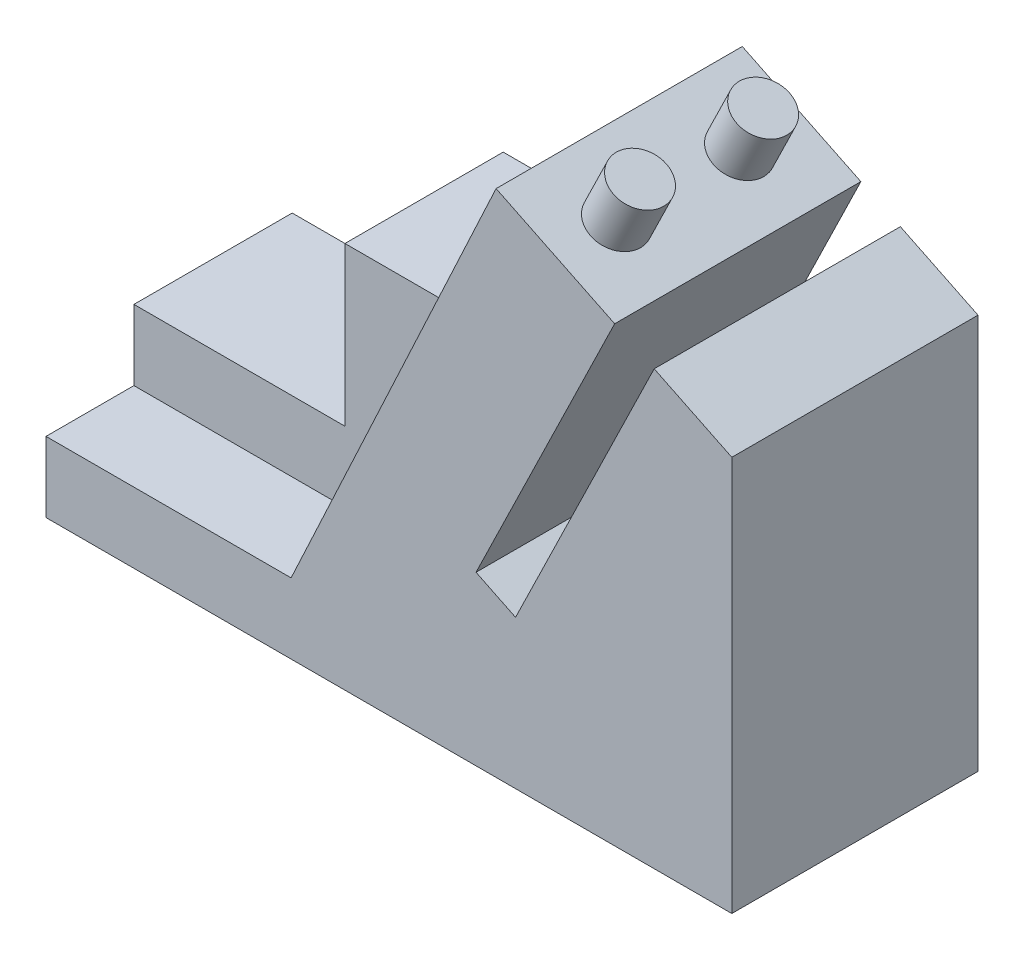
SolidWorks part; units mm, degrees
ref_plane "Front Plane" through (0, 0, 0) normal (0, 0, 1) x (1, 0, 0)
ref_plane "Top Plane" through (0, 0, 0) normal (0, 1, 0) x (1, 0, 0)
ref_plane "Right Plane" through (0, 0, 0) normal (1, 0, 0) x (0, 0, -1)
sketch "Sketch1" plane through (0, 0, 0) normal (0, 0, 1) x (1, 0, 0)
  line L0 (0, 0) -> (78, 0)
  line L1 (0, 0) -> (0, 8)
  line L2 (0, 8) -> (27.876, 8)
  line L3 (27.876, 8) -> (51.1914, 58)
  line L4 (78, 0) -> (78, 44.9394)
  line L6 (51.1914, 58) -> (64.6762, 51.4305)
  line L7 (64.6762, 51.4305) -> (48.9093, 19.0668)
  line L8 (48.9093, 19.0668) -> (53.4043, 16.877)
  line L9 (53.4043, 16.877) -> (69.1712, 49.2406)
  line L10 (69.1712, 49.2406) -> (78, 44.9394)
  dimension "D1" = 8
  dimension "D2" = 65
  dimension "D3" = 78
  dimension "D4" = 58
  dimension "D5" = 5
  dimension "D6" = 36
  dimension "D7" = 15
extrude "Boss-Extrude1" add sketch "Sketch1" along normal blind 28
sketch "Sketch2" plane through (0, 0, 0) normal (0, 0, -1) x (-1, 0, 0)
  line L0 (0, 8) -> (0, 16)
  line L1 (0, 16) -> (-24, 16)
  line L2 (-24, 16) -> (-24, 34)
  line L3 (-24, 34) -> (-40, 34)
  line L4 (-51.1914, 58) -> (-27.876, 8) construction
  line L5 (-40, 34) -> (-27.876, 8)
  line L6 (-27.876, 8) -> (0, 8)
  dimension "D1" = 8
  dimension "D2" = 24
  dimension "D3" = 18
  dimension "D4" = 16
extrude "Boss-Extrude2" add sketch "Sketch2" against normal blind 18
sketch "Sketch3" plane through (32.6557, 67.0302, 0) normal (0.438, 0.899, 0) x (0.899, -0.438, 0)
  line L0 (35.6183, -28) -> (20.6183, -28) construction
  line L1 (35.6183, -28) -> (35.6183, 0) construction
  line L2 (20.6183, -28) -> (20.6183, 0) construction
  line L3 (35.6183, 0) -> (20.6183, 0) construction
  circle A0 centre (28.1183, -21) radius 3
  circle A1 centre (28.1183, -7) radius 3
  dimension "D1" = 6
  dimension "D2" = 6
  dimension "D3" = 7
  dimension "D4" = 7.5
  dimension "D5" = 7.5
  dimension "D6" = 7
extrude "Boss-Extrude3" add sketch "Sketch3" along normal blind 6
